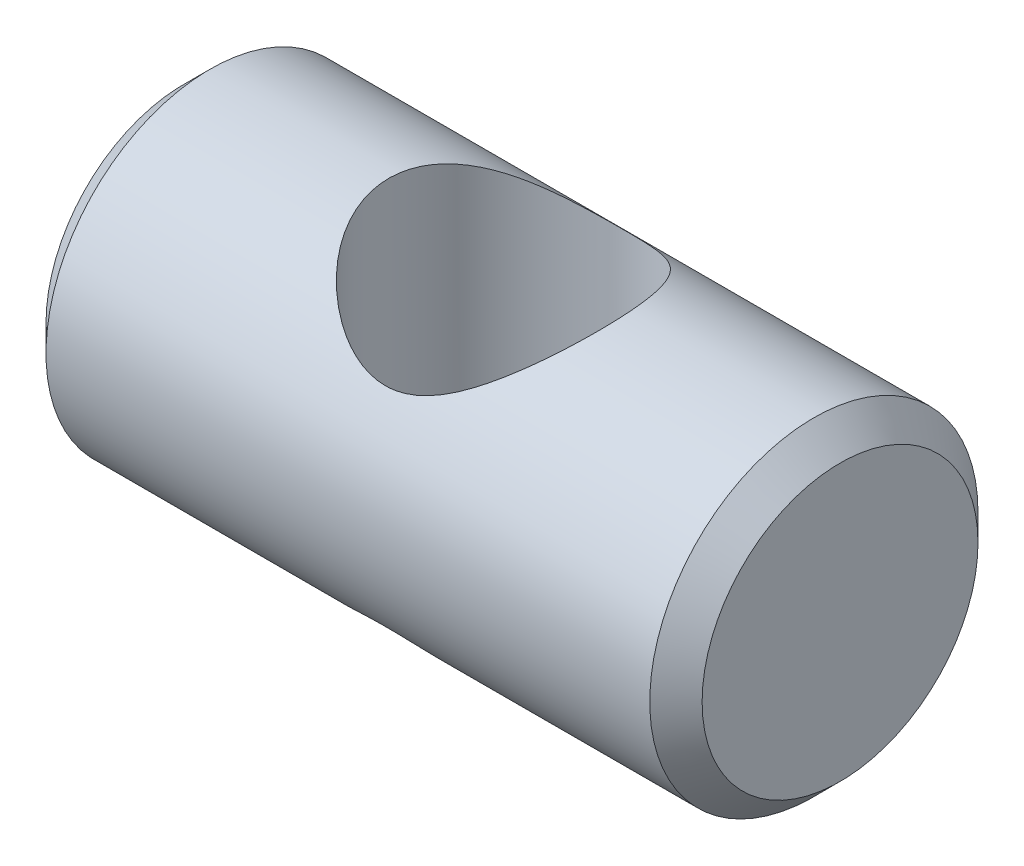
SolidWorks part; units mm, degrees
ref_plane "Front Plane" through (0, 0, 0) normal (0, 0, 1) x (1, 0, 0)
ref_plane "Top Plane" through (0, 0, 0) normal (0, 1, 0) x (1, 0, 0)
ref_plane "Right Plane" through (0, 0, 0) normal (1, 0, 0) x (0, 0, -1)
sketch "Sketch1" plane through (0, 0, 0) normal (1, 0, 0) x (0, 0, -1)
  circle A0 centre (0, 0) radius 4.765
  dimension "D1" = 9.53
extrude "Boss-Extrude1" add sketch "Sketch1" along normal mid plane 19.05
chamfer "Chamfer1" distance 0.76 angle 45 2 edges at (-9.525, 0, -4.765) (9.525, 0, -4.765)
sketch "Sketch2" plane through (0, 0, 0) normal (0, 1, 0) x (1, 0, 0)
  circle A0 centre (0, -0.25) radius 3.43
  point P2 (0, 0)
  dimension "D1" = 6.86
  dimension "D2" = 0.25
extrude "Cut-Extrude1" cut sketch "Sketch2" against normal mid plane 19.05
